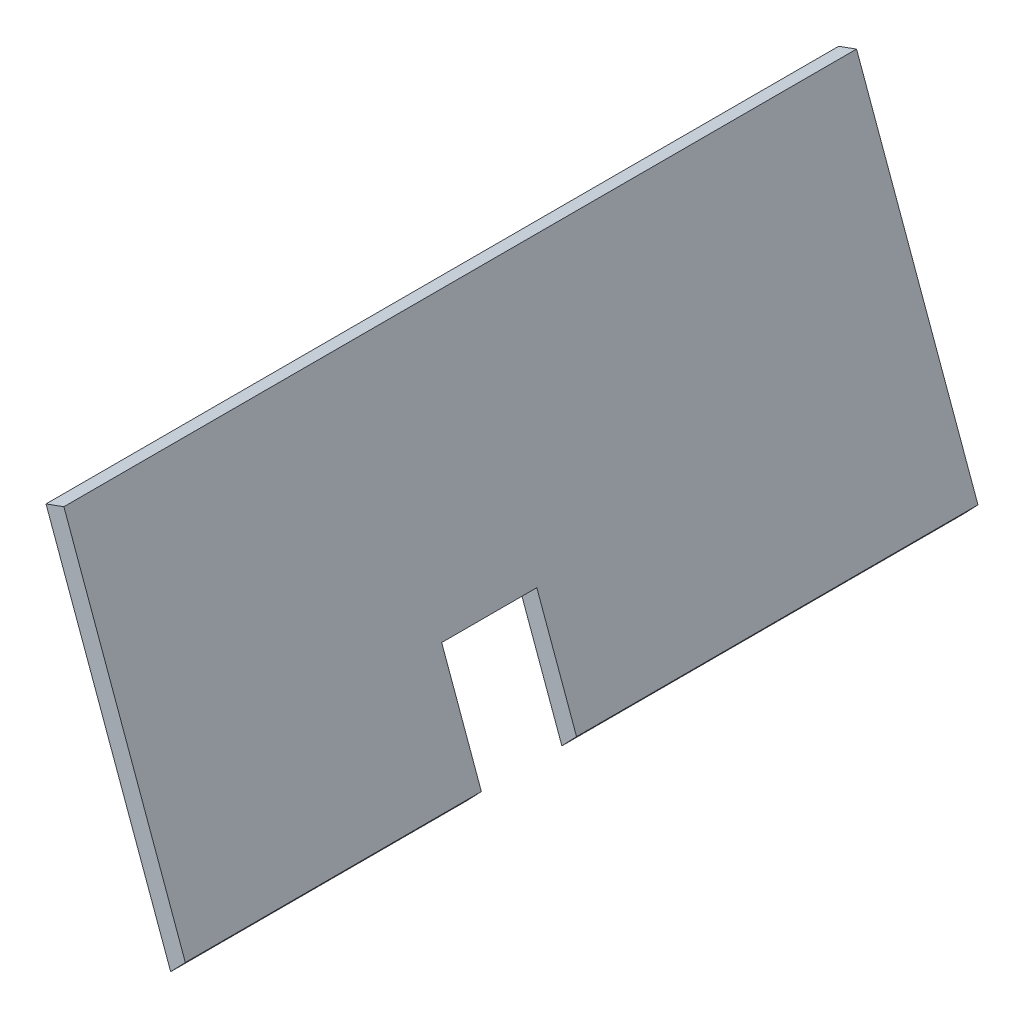
SolidWorks part; units mm, degrees
ref_plane "Front Plane" through (0, 0, 0) normal (0, 0, 1) x (1, 0, 0)
ref_plane "Top Plane" through (0, 0, 0) normal (0, 1, 0) x (1, 0, 0)
ref_plane "Right Plane" through (0, 0, 0) normal (1, 0, 0) x (0, 0, -1)
sketch "Sketch2" plane through (0, 0, 2) normal (0, 0, 1) x (1, 0, 0)
  line L1 (3386.1293, -6568.6757) -> (3418.8901, -6658.7625)
  line L4 (3386.1293, -6568.6757) -> (3390.8283, -6566.9669)
  line L7 (3418.8901, -6658.7625) -> (3422.7445, -6654.7315)
  line L9 (3390.8283, -6566.9669) -> (3422.7445, -6654.7315)
  line L19 (3387.8112, -6643.7718) -> (3753.2487, -6758.4209) construction
  line L20 (3386.3144, -6648.5426) -> (3751.752, -6763.1916) construction
  circle A0 centre (3470.925, -6604.3435) radius 62.5 construction
  circle A1 centre (3470.925, -6604.3435) radius 67.5 construction
extrude "Boss-Extrude1" add sketch "Sketch2" along normal up to surface (208.2958 mm away)
sketch "Sketch3" plane through (885.5869, 322.0501, 0) normal (0.9398, 0.3418, 0) x (0, 0, -1)
  line L0 (-107.5, -7393.2606) -> (-132.5, -7393.2606)
  line L1 (-107.5, -7393.2606) -> (-107.5, -7426.2606)
  line L2 (-132.5, -7393.2606) -> (-132.5, -7426.2606)
  line L3 (-107.5, -7426.2606) -> (-132.5, -7426.2606)
  line L4 (-107.5, -7455.4018) -> (-107.5, -7392.9018) construction
  line L5 (-132.5, -7392.9018) -> (-132.5, -7467.5951) construction
  line L6 (-210.2958, -7426.2606) -> (-2, -7426.2606) construction
  dimension "D1" = 33
extrude "Cut-Extrude1" cut sketch "Sketch3" against normal through all
